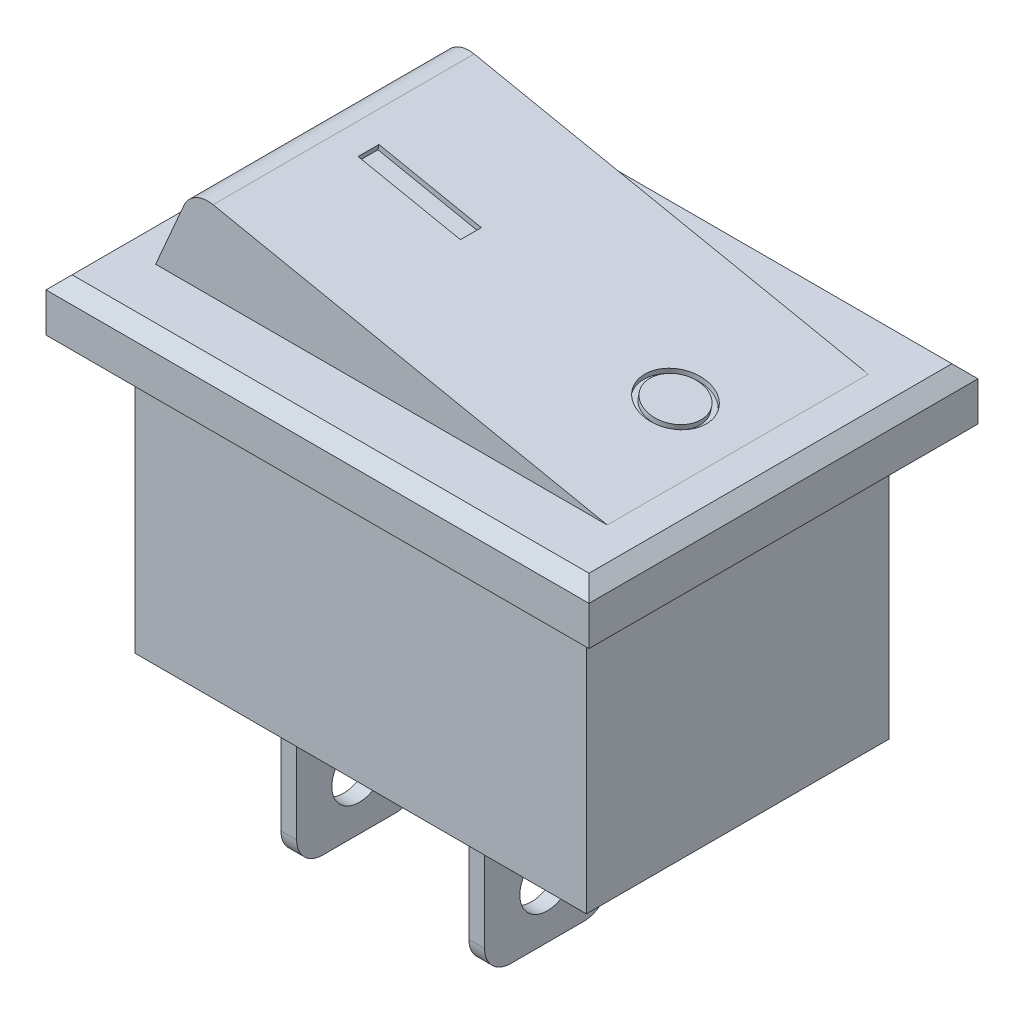
SolidWorks part; units mm, degrees
ref_plane "前视基准面" through (0, 0, 0) normal (0, 0, 1) x (1, 0, 0)
ref_plane "上视基准面" through (0, 0, 0) normal (0, 1, 0) x (1, 0, 0)
ref_plane "右视基准面" through (0, 0, 0) normal (1, 0, 0) x (0, 0, -1)
sketch "草图1" plane through (0, 0, 0) normal (0, 1, 0) x (1, 0, 0)
  line L1 (-8.65, 5.8) -> (8.65, 5.8)
  line L2 (-8.65, 5.8) -> (-8.65, -5.8)
  line L3 (-8.65, -5.8) -> (8.65, -5.8)
  line L4 (8.65, 5.8) -> (8.65, -5.8)
  line L5 (-8.65, 5.8) -> (8.65, -5.8) construction
  line L6 (-8.65, -5.8) -> (8.65, 5.8) construction
  point P0 (0, 0)
  dimension "D1" = 17.3
  dimension "D2" = 11.6
extrude "凸台-拉伸1" add sketch "草图1" along normal blind 10.5
sketch "草图2" plane through (0, 10.5, 0) normal (0, 1, 0) x (1, 0, 0)
  line L1 (-10.4, 7.45) -> (10.4, 7.45)
  line L2 (-10.4, 7.45) -> (-10.4, -7.45)
  line L3 (-10.4, -7.45) -> (10.4, -7.45)
  line L4 (10.4, 7.45) -> (10.4, -7.45)
  line L5 (-10.4, 7.45) -> (10.4, -7.45) construction
  line L6 (-10.4, -7.45) -> (10.4, 7.45) construction
  point P0 (0, 0)
  dimension "D1" = 20.8
  dimension "D2" = 14.9
extrude "凸台-拉伸2" add sketch "草图2" along normal blind 2
chamfer "倒角1" distance 0.5 angle 45 4 edges at (10.4, 12.5, 0) (0, 12.5, 7.45) (0, 12.5, -7.45) (-10.4, 12.5, 0)
sketch "草图3" plane through (0, 0, 0) normal (0, -1, 0) x (1, 0, 0)
  line L0 (-8.65, -5.8) -> (-8.65, 5.8) construction
  line L1 (-6.45, 2.4) -> (-5.85, 2.4)
  line L2 (-6.45, 2.4) -> (-6.45, -2.4)
  line L3 (-6.45, -2.4) -> (-5.85, -2.4)
  line L4 (-5.85, 2.4) -> (-5.85, -2.4)
  line L5 (0.75, 2.4) -> (1.35, 2.4)
  line L6 (0.75, 2.4) -> (0.75, -2.4)
  line L7 (0.75, -2.4) -> (1.35, -2.4)
  line L8 (1.35, 2.4) -> (1.35, -2.4)
  line L9 (-8.65, 5.8) -> (8.65, 5.8) construction
  dimension "D1" = 0.6
  dimension "D2" = 0.6
  dimension "D3" = 4.8
  dimension "D4" = 4.8
  dimension "D5" = 2.2
  dimension "D6" = 6.6
  dimension "D7" = 3.4
  dimension "D8" = 3.4
extrude "凸台-拉伸3" add sketch "草图3" along normal blind 7.5
sketch "草图4" plane through (-6.45, 0, 0) normal (-1, 0, 0) x (0, 0, 1)
  line L0 (2.4, -7.5) -> (-2.4, -7.5) construction
  circle A0 centre (0, -5.4) radius 1.05
  dimension "D1" = 2.1
  dimension "D2" = 2.1
extrude "切除-拉伸1" cut sketch "草图4" against normal through all
fillet "圆角1" radius 1 4 edges at (1.05, -7.5, -2.4) (1.05, -7.5, 2.4) (-6.15, -7.5, 2.4) (-6.15, -7.5, -2.4)
sketch "草图6" plane through (0, 0, 0) normal (0, 0, 1) x (1, 0, 0)
  line L0 (-8.65, 12.5) -> (-7.5672, 14.993)
  line L1 (-9.9, 12.5) -> (9.9, 12.5) construction
  line L2 (-6.4505, 15.5746) -> (8.65, 12.5)
  line L3 (-8.65, 10.5) -> (-8.65, 0) construction
  line L4 (8.65, 10.5) -> (8.65, 0) construction
  line L5 (9.9, 12.5) -> (8.65, 12.5)
  line L9 (-9.9, 12.5) -> (-10.4, 12)
  line L10 (-10.4, 12) -> (10.4, 12)
  line L11 (10.4, 12) -> (9.9, 12.5)
  line L12 (9.9, 12.5) -> (-9.9, 12.5)
  line L13 (-9.9, 12.5) -> (-10.4, 12)
  line L14 (-10.4, 12) -> (10.4, 12)
  line L15 (10.4, 12) -> (9.9, 12.5)
  line L16 (-8.65, 12.5) -> (-9.9, 12.5)
  arc A0 (-7.5672, 14.993) -> (-6.4505, 15.5746) centre (-6.65, 14.5947) cw
  point P6 (0, 0)
  point P12 (-6.8941, 16.4127)
  point P13 (-5.65, 17.6272)
  point P14 (-7.6288, 17.3757)
  point P15 (-6.4505, 15.5746)
  dimension "D4" = 1
  dimension "D1" = 0
  dimension "D2" = 0
  dimension "D3" = 2
  dimension "D5" = 0
extrude "凸台-拉伸4" add sketch "草图6" along normal mid plane 10
sketch "草图7" plane through (2.7881, 13.6935, 0) normal (0.1995, 0.9799, 0) x (0.9799, -0.1995, 0)
  line L0 (-9.4281, -5) -> (-9.4281, 5) construction
  line L1 (-8.4281, 0.3755) -> (-4.4281, 0.3755)
  line L2 (-8.4281, 0.3755) -> (-8.4281, -0.4245)
  line L3 (-8.4281, -0.4245) -> (-4.4281, -0.4245)
  line L4 (-4.4281, 0.3755) -> (-4.4281, -0.4245)
  line L5 (-8.4281, 0.3755) -> (-4.4281, -0.4245) construction
  line L6 (-8.4281, -0.4245) -> (-4.4281, 0.3755) construction
  circle A0 centre (3.5461, 0) radius 1
  circle A1 centre (3.5461, 0) radius 1.2
  point P3 (-6.4281, -0.0245)
  dimension "D1" = 2
  dimension "D2" = 2.4
  dimension "D3" = 4
  dimension "D4" = 0.8
  dimension "D5" = 1
extrude "切除-拉伸2" cut sketch "草图7" against normal blind 0.2
